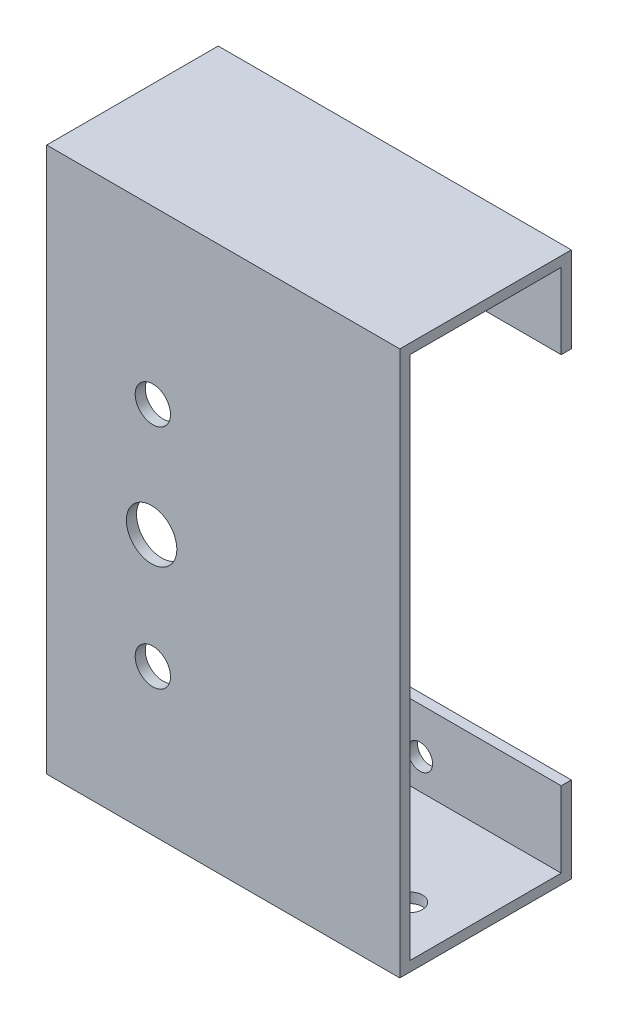
SolidWorks part; units mm, degrees
material "Liga 1060"
ref_plane "Plano frontal" through (0, 0, 0) normal (0, 0, 1) x (1, 0, 0)
ref_plane "Plano superior" through (0, 0, 0) normal (0, 1, 0) x (1, 0, 0)
ref_plane "Plano direito" through (0, 0, 0) normal (1, 0, 0) x (0, 0, -1)
sketch "Esboço1" plane through (0, 0, 0) normal (0, 0, 1) x (1, 0, 0)
  line L1 (35, -54) -> (-35, -54)
  line L2 (35, -54) -> (35, 54)
  line L3 (35, 54) -> (-35, 54)
  line L4 (-35, -54) -> (-35, 54)
  line L5 (35, -54) -> (-35, 54) construction
  line L6 (35, 54) -> (-35, -54) construction
  point P0 (0, 0)
  dimension "D1" = 70
  dimension "D2" = 108
extrude "Ressalto-extrusão1" add sketch "Esboço1" along normal blind 2
sketch "Esboço2" plane through (0, 0, 0) normal (0, 0, -1) x (-1, 0, 0)
  line L0 (35, 54) -> (35, -54) construction
  line L1 (-35, -54) -> (35, -54)
  line L2 (-35, -54) -> (-35, -52)
  line L3 (-35, -52) -> (35, -52)
  line L4 (35, -54) -> (35, -52)
  dimension "D1" = 2
extrude "Ressalto-extrusão2" add sketch "Esboço2" along normal blind 30
sketch "Esboço3" plane through (0, 0, -30) normal (0, 0, -1) x (-1, 0, 0)
  line L0 (35, 54) -> (35, -52) construction
  line L1 (-35, -54) -> (35, -54)
  line L2 (-35, -54) -> (-35, -37)
  line L3 (-35, -37) -> (35, -37)
  line L4 (35, -54) -> (35, -37)
  dimension "D1" = 17
extrude "Ressalto-extrusão3" add sketch "Esboço3" along normal blind 2
mirror "Espelhar1" about plane through (0, 0, 0) normal (0, 1, 0) of "Ressalto-extrusão3", "Ressalto-extrusão2"
sketch "Esboço4" plane through (0, 0, -30) normal (0, 0, 1) x (1, 0, 0)
  circle A0 centre (7, -46) radius 2.5 construction
  circle A1 centre (18.3, 42.5) radius 2.5 construction
  circle A2 centre (7, -46) radius 2.5
  circle A3 centre (18.3, 42.5) radius 2.5
extrude "Corte-extrusão1" cut sketch "Esboço4" against normal blind 10
sketch "Esboço5" plane through (0, 0, -32) normal (0, 0, -1) x (-1, 0, 0)
  line L0 (18.7, 0) -> (-18.7, 0) construction
  line L1 (-35, 54) -> (35, 54) construction
  line L4 (35, 54) -> (35, 37) construction
  circle A0 centre (25, 44) radius 2.5
  circle A1 centre (25, -44) radius 2.5
  point P3 (-18.3, 42.5)
  point P10 (-7, -46)
  dimension "D1" = 5
  dimension "D2" = 10
  dimension "D3" = 10
extrude "Corte-extrusão2" [suppressed] cut sketch "Esboço5" against normal blind 2
sketch "Esboço6" [suppressed] plane through (0, 0, 2) normal (0, 0, 1) x (1, 0, 0)
  circle A0 centre (7, -46) radius 2.5 construction
  circle A1 centre (-25, 44) radius 2.5 construction
  circle A2 centre (18.3, 42.5) radius 2.5 construction
  circle A3 centre (7, -46) radius 2.5
  circle A4 centre (-25, 44) radius 2.5
  circle A5 centre (18.3, 42.5) radius 2.5
extrude "Corte-extrusão3" [suppressed] cut sketch "Esboço6" against normal blind 2
sketch "Esboço7" [suppressed] plane through (0, 0, 2) normal (0, 0, 1) x (1, 0, 0)
  circle A0 centre (-25, -44) radius 2.5 construction
  circle A1 centre (-25, -44) radius 2.5
extrude "Corte-extrusão4" [suppressed] cut sketch "Esboço7" against normal blind 2
sketch "Esboço8" plane through (0, -52, 0) normal (0, 1, 0) x (1, 0, 0)
  line L0 (35, -2) -> (35, 32) construction
  line L1 (35, 32) -> (-35, 32) construction
  line L3 (0, -18.7) -> (0, 18.7) construction
  circle A0 centre (25, 10) radius 2.5
  circle A1 centre (-25, 10) radius 2.5
  dimension "D1" = 5
  dimension "D2" = 10
  dimension "D3" = 22
extrude "Corte-extrusão5" cut sketch "Esboço8" against normal blind 10
sketch "Esboço9" plane through (0, 0, 2) normal (0, 0, 1) x (1, 0, 0)
  circle A0 centre (-14.2, -2.5) radius 5 construction
  circle A1 centre (-14.2, -2.5) radius 5
extrude "Corte-extrusão6" cut sketch "Esboço9" against normal blind 10
sketch "Esboço15" plane through (0, 0, 2) normal (0, 0, 1) x (1, 0, 0)
  circle A0 centre (-13.9545, 20) radius 3.5
  circle A1 centre (-14.2, -2.5) radius 5 construction
  circle A2 centre (-13.9545, -25) radius 3.5
  dimension "D2" = 7
  dimension "D3" = 22.5
  dimension "D4" = 7
  dimension "D1" = 22.5
extrude "Corte-extrusão7" cut sketch "Esboço15" against normal blind 10
sketch "Sketch1" plane through (0, 0, -32) normal (0, 0, -1) x (-1, 0, 0)
  line L0 (-35, 54) -> (35, 54) construction
  line L1 (35, 54) -> (35, 37) construction
  line L2 (35, -54) -> (35, -37) construction
  line L3 (-35, -54) -> (35, -54) construction
  circle A0 centre (25.5, 44.5) radius 2.5
  circle A1 centre (25.5, -44.5) radius 2.5
  point P8 (35, 45.5)
  dimension "D1" = 5
  dimension "D2" = 5
  dimension "D5" = 9.5
  dimension "D6" = 9.5
  dimension "D3" = 9.5
  dimension "D4" = 9.5
extrude "Cut-Extrude1" cut sketch "Sketch1" against normal up to next
